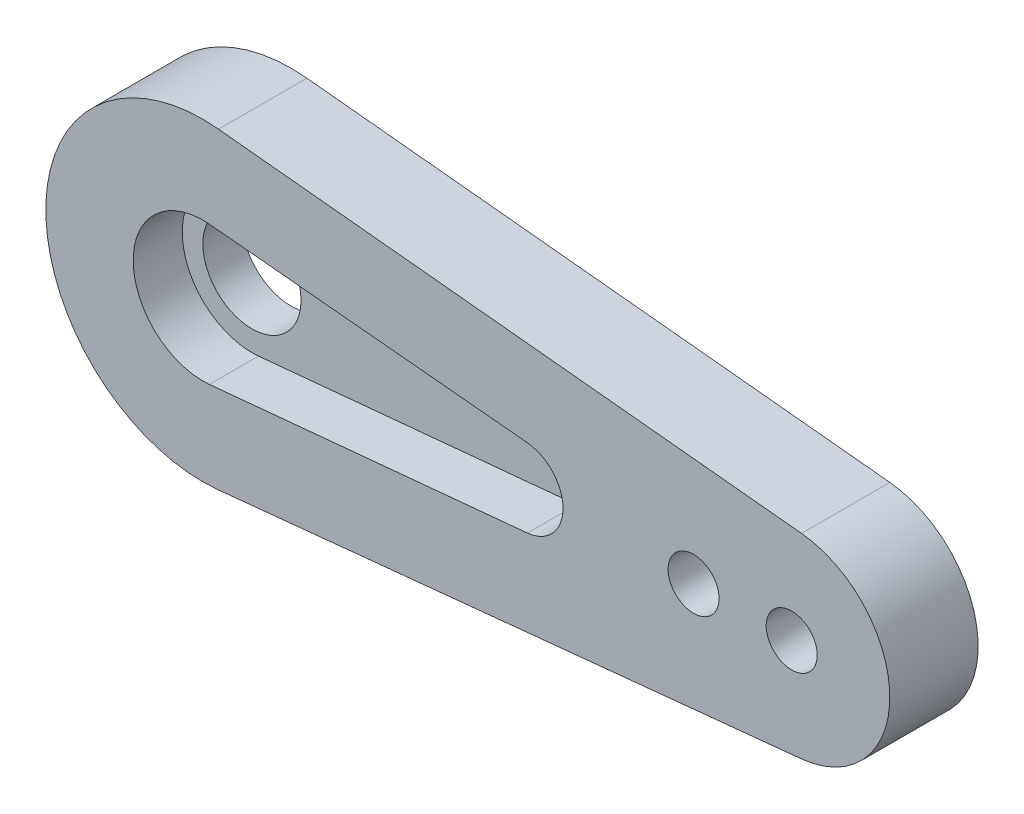
SolidWorks part; units mm, degrees
ref_plane "Front Plane" through (0, 0, 0) normal (0, 0, 1) x (1, 0, 0)
ref_plane "Top Plane" through (0, 0, 0) normal (0, 1, 0) x (1, 0, 0)
ref_plane "Right Plane" through (0, 0, 0) normal (1, 0, 0) x (0, 0, -1)
sketch "Esquisse1" plane through (0, 0, 0) normal (0, 0, 1) x (1, 0, 0)
  line L0 (-3.55, 0) -> (-3.55, 5.3986) construction
  line L1 (0.3365, 3.534) -> (16.5396, 1.991)
  line L2 (16.5396, -1.991) -> (0.3365, -3.534)
  line L3 (18.35, 0) -> (18.35, 4.9554) construction
  line L4 (0.8, 7.9599) -> (30.5, 4.9749)
  line L5 (0.8, -7.9599) -> (30.5, -4.9749)
  arc A0 (0.3365, 3.534) -> (0.3365, -3.534) centre (0, 0) ccw
  arc A1 (16.5396, -1.991) -> (16.5396, 1.991) centre (16.35, 0) ccw
  arc A3 (0.8, -7.9599) -> (0.8, 7.9599) centre (0, 0) cw
  arc A4 (30.5, 4.9749) -> (30.5, -4.9749) centre (30, 0) cw
  dimension "D2" = 3.55
  dimension "D3" = 2
  dimension "D6" = 8
  dimension "D8" = 5
  dimension "D1" = 21.9
  dimension "D7" = 30
extrude "Main" add sketch "Esquisse1" along normal blind 2.5
sketch "Esquisse2" plane through (0, 0, 0) normal (0, 0, -1) x (-1, 0, 0)
  line L0 (-0.8, -7.9599) -> (-30.5, -4.9749)
  line L1 (-0.8, -7.9599) -> (-30.5, -4.9749) construction
  line L3 (-0.8, 7.9599) -> (-30.5, 4.9749)
  arc A0 (-30.5, 4.9749) -> (-30.5, -4.9749) centre (-30, 0) ccw construction
  circle A2 centre (0, 0) radius 2.5
  arc A3 (-0.8, -7.9599) -> (-0.8, 7.9599) centre (0, 0) ccw
  arc A5 (-30.5, 4.9749) -> (-30.5, -4.9749) centre (-30, 0) ccw
  dimension "D1" = 5
extrude "OriginalBracket" add sketch "Esquisse2" along normal blind 2
sketch "Esquisse3" plane through (0, 0, 2.5) normal (0, 0, 1) x (1, 0, 0)
  circle A0 centre (30, 0) radius 1.3
  arc A2 (30.5, -4.9749) -> (30.5, 4.9749) centre (30, 0) ccw construction
  circle A3 centre (25, 0) radius 1.3
  dimension "D1" = 2.6
  dimension "D2" = 5
  dimension "D3" = 30
extrude "FixingHole" cut sketch "Esquisse3" against normal through all
